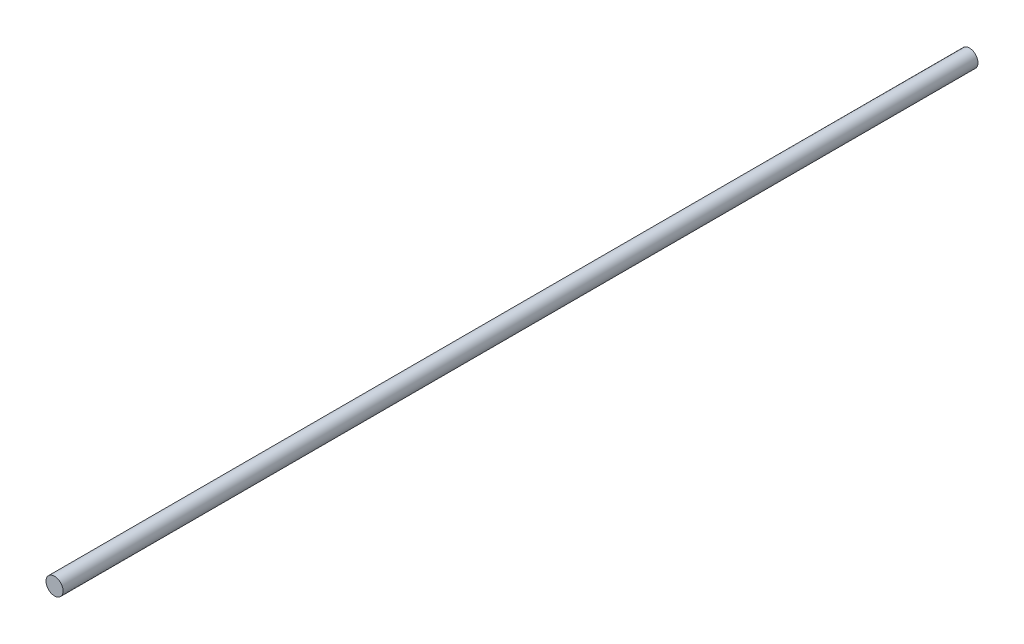
SolidWorks part; units mm, degrees
ref_plane "Front Plane" through (0, 0, 0) normal (0, 0, 1) x (1, 0, 0)
ref_plane "Top Plane" through (0, 0, 0) normal (0, 1, 0) x (1, 0, 0)
ref_plane "Right Plane" through (0, 0, 0) normal (1, 0, 0) x (0, 0, -1)
sketch "Sketch1" plane through (0, 0, 0) normal (0, 0, 1) x (1, 0, 0)
  circle A0 centre (0, 0) radius 4
  dimension "D1" = 8
extrude "Boss-Extrude1" add sketch "Sketch1" along normal blind 428
